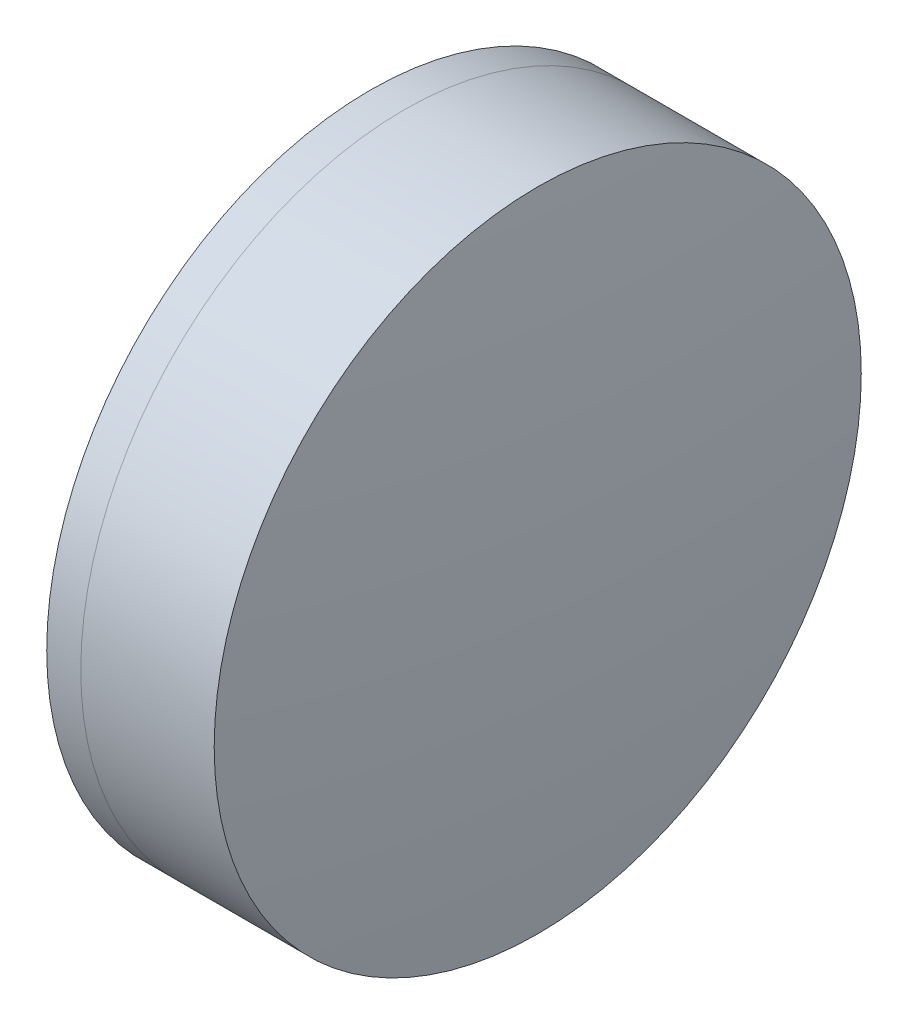
SolidWorks part; units mm, degrees
ref_plane "前视基准面" through (0, 0, 0) normal (0, 0, 1) x (1, 0, 0)
ref_plane "上视基准面" through (0, 0, 0) normal (0, 1, 0) x (1, 0, 0)
ref_plane "右视基准面" through (0, 0, 0) normal (1, 0, 0) x (0, 0, -1)
sketch "草图1" plane through (0, 0, 0) normal (0, 1, 0) x (1, 0, 0)
  line L0 (-0.8161, 0) -> (118.0272, 0) construction
  line L1 (88.9919, -25.4) -> (91.6651, -25.4)
  line L2 (88.9919, 25.4) -> (91.6651, 25.4)
  arc A0 (91.6651, -25.4) -> (91.6651, 25.4) centre (61.952, 0) ccw
  arc A1 (88.9919, 25.4) -> (88.9919, -25.4) centre (131.932, 0) ccw
  point P10 (82.042, 0)
  point P11 (101.042, 0)
  dimension "D3" = 49.89
  dimension "D4" = 39.09
  dimension "D1" = 25.4
  dimension "D2" = 25.4
  dimension "D5" = 19
revolve "旋转1" add sketch "草图1" angle 360 about L0
sketch "草图2" plane through (0, 0, 0) normal (0, 1, 0) x (1, 0, 0)
  line L0 (-0.5519, 0) -> (162.8134, 0) construction
  line L2 (91.6651, 25.4) -> (102.1395, 25.4)
  line L3 (91.6651, -25.4) -> (102.1395, -25.4)
  arc A0 (102.1395, -25.4) -> (102.1395, 25.4) centre (-127.158, 0) ccw
  arc A1 (91.6651, -25.4) -> (91.6651, 25.4) centre (61.952, 0) ccw construction
  arc A2 (91.6651, -25.4) -> (91.6651, 25.4) centre (61.952, 0) ccw
  point P4 (101.042, 0)
  point P8 (103.542, 0)
  point P9 (4.1213, 0)
  dimension "D1" = 230.7
  dimension "D2" = 2.5
revolve "旋转2" add sketch "草图2" angle 360 about L0
